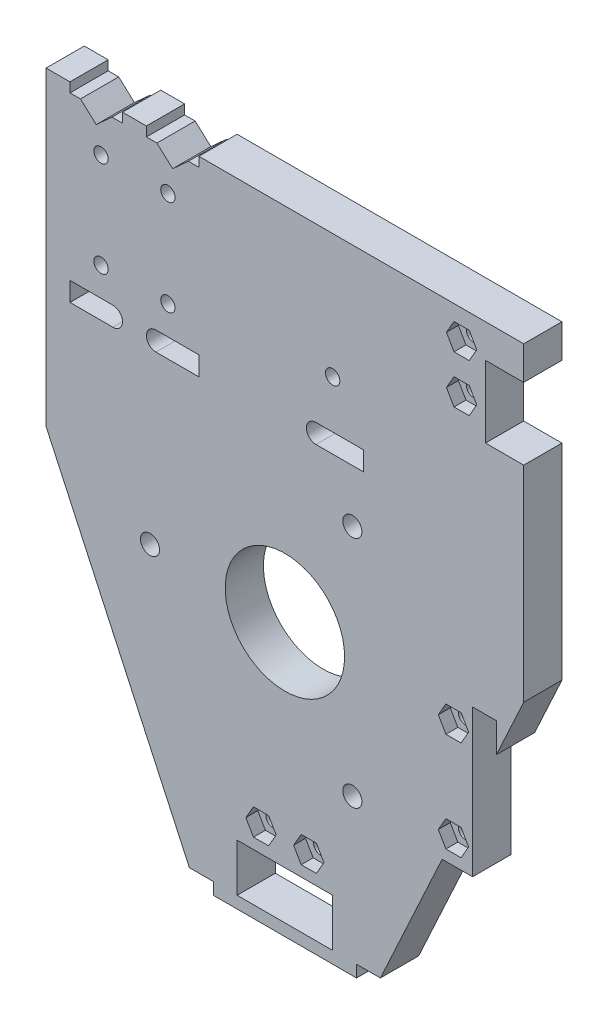
SolidWorks part; units mm, degrees
material "1060 合金"
ref_plane "前视基准面" through (0, 0, 0) normal (0, 0, 1) x (1, 0, 0)
ref_plane "上视基准面" through (0, 0, 0) normal (0, 1, 0) x (1, 0, 0)
ref_plane "右视基准面" through (0, 0, 0) normal (1, 0, 0) x (0, 0, -1)
sketch "草图1" plane through (0, 0, 0) normal (0, 0, 1) x (1, 0, 0)
  line L1 (0, 0) -> (100, 0)
  line L2 (0, 0) -> (0, 130)
  line L3 (0, 130) -> (100, 130)
  line L4 (100, 0) -> (100, 130)
  dimension "D1" = 100
  dimension "D2" = 130
extrude "凸台-拉伸1" add sketch "草图1" along normal blind 8
sketch "草图2" plane through (0, 0, 8) normal (0, 0, 1) x (1, 0, 0)
  line L0 (0, 130) -> (0, 0) construction
  line L1 (0, 0) -> (100, 0) construction
  circle A0 centre (50, 54.5) radius 25
  dimension "D1" = 50
  dimension "D2" = 50
  dimension "D3" = 54.5
sketch "草图3" plane through (0, 0, 8) normal (0, 0, 1) x (1, 0, 0)
  line L0 (0, 0) -> (100, 0) construction
  line L1 (40, 0) -> (60, 0)
  line L2 (40, 0) -> (40, 10)
  line L3 (40, 10) -> (60, 10)
  line L4 (60, 0) -> (60, 10)
  line L5 (0, 130) -> (0, 0) construction
  line L6 (0, 0) -> (30, 0)
  line L7 (30, 0) -> (0, 65)
  line L8 (0, 65) -> (0, 0)
  line L9 (100, 0) -> (100, 65)
  line L10 (100, 0) -> (100, 130) construction
  line L11 (100, 65) -> (70, 0)
  line L12 (70, 0) -> (100, 0)
  dimension "D1" = 20
  dimension "D2" = 10
  dimension "D3" = 40
  dimension "D4" = 30
  dimension "D5" = 30
extrude "切除-拉伸1" cut sketch "草图3" against normal blind 8
sketch "草图4" plane through (0, 0, 0) normal (0, 0, -1) x (-1, 0, 0)
  line L0 (-56.5, 94) -> (-66.5, 94)
  line L1 (-100, 65) -> (-100, 130) construction
  line L2 (-100, 108) -> (-92, 108)
  line L3 (-100, 108) -> (-100, 123)
  line L4 (-100, 123) -> (-92, 123)
  line L5 (-66.5, 94) -> (-66.5, 90)
  line L6 (-66.5, 90) -> (-56.5, 90)
  line L7 (-32, 94) -> (-32, 90)
  line L8 (-32, 90) -> (-23, 90)
  line L9 (-23, 94) -> (-32, 94)
  line L10 (-5, 94) -> (-5, 90)
  line L11 (-5, 90) -> (-14, 90)
  line L12 (-14, 94) -> (-5, 94)
  line L13 (-10.5, 125) -> (-13.8, 128)
  line L14 (-100, 130) -> (0, 130) construction
  line L15 (-13.8, 128) -> (-10.5, 125) construction
  line L16 (-16, 130) -> (-5, 130)
  line L17 (-10.5, 125) -> (-7.2, 128) construction
  line L18 (-7.2, 128) -> (-10.5, 125)
  line L19 (-26.5, 125) -> (-29.8, 128)
  line L20 (-29.8, 128) -> (-26.5, 125) construction
  line L21 (-32, 130) -> (-21, 130)
  line L22 (-26.5, 125) -> (-23.2, 128) construction
  line L23 (-23.2, 128) -> (-26.5, 125)
  line L24 (-21, 130) -> (-21, 128)
  line L25 (-92, 108) -> (-92, 123)
  line L26 (-100, 108) -> (-80, 108) construction
  line L27 (-21, 128) -> (-23.2, 128)
  line L28 (-32, 128) -> (-32, 130)
  line L29 (-29.8, 128) -> (-32, 128)
  line L30 (-5, 130) -> (-5, 128)
  line L31 (-5, 128) -> (-7.2, 128)
  line L32 (-60, 10) -> (-40, 10) construction
  line L33 (-13.8, 128) -> (-16, 128)
  line L34 (-16, 128) -> (-16, 130)
  line L35 (-40, 10) -> (-40, 0) construction
  line L36 (-60, 0) -> (-60, 10) construction
  arc A0 (-56.5, 90) -> (-56.5, 94) centre (-56.5, 92) ccw
  arc A1 (-23, 90) -> (-23, 94) centre (-23, 92) ccw
  arc A2 (-14, 90) -> (-14, 94) centre (-14, 92) cw
  circle A4 centre (-87, 124) radius 1.5
  circle A5 centre (-25.5, 100) radius 1.5
  circle A6 centre (-11.5, 100) radius 1.5
  circle A7 centre (-11.5, 120) radius 1.5
  circle A8 centre (-25.5, 120) radius 1.5
  circle A9 centre (-60, 104) radius 1.5
  circle A10 centre (-45, 15) radius 1.5
  circle A11 centre (-55, 15) radius 1.5
  circle A15 centre (-87, 114) radius 1.5
  dimension "D1" = 5
  dimension "D2" = 5
  dimension "D3" = 5
  dimension "D4" = 5
extrude "切除-拉伸2" cut sketch "草图4" against normal through all
sketch "草图9" plane through (0, 0, 8) normal (0, 0, 1) x (1, 0, 0)
  line L1 (90.1754, 124) -> (88.5877, 126.75)
  line L2 (88.5877, 126.75) -> (85.4123, 126.75)
  line L3 (85.4123, 126.75) -> (83.8246, 124)
  line L4 (83.8246, 124) -> (85.4123, 121.25)
  line L5 (85.4123, 121.25) -> (88.5877, 121.25)
  line L6 (88.5877, 121.25) -> (90.1754, 124)
  line L7 (90.1754, 114) -> (88.5877, 116.75)
  line L8 (88.5877, 116.75) -> (85.4123, 116.75)
  line L9 (85.4123, 116.75) -> (83.8246, 114)
  line L10 (83.8246, 114) -> (85.4123, 111.25)
  line L11 (85.4123, 111.25) -> (88.5877, 111.25)
  line L12 (88.5877, 111.25) -> (90.1754, 114)
  line L13 (48.1754, 15) -> (46.5877, 17.75)
  line L14 (46.5877, 17.75) -> (43.4123, 17.75)
  line L15 (43.4123, 17.75) -> (41.8246, 15)
  line L16 (41.8246, 15) -> (43.4123, 12.25)
  line L17 (43.4123, 12.25) -> (46.5877, 12.25)
  line L18 (46.5877, 12.25) -> (48.1754, 15)
  line L19 (58.1754, 15) -> (56.5877, 17.75)
  line L20 (56.5877, 17.75) -> (53.4123, 17.75)
  line L21 (53.4123, 17.75) -> (51.8246, 15)
  line L22 (51.8246, 15) -> (53.4123, 12.25)
  line L23 (53.4123, 12.25) -> (56.5877, 12.25)
  line L24 (56.5877, 12.25) -> (58.1754, 15)
  circle A0 centre (45, 15) radius 2.75 construction
  circle A1 centre (55, 15) radius 2.75 construction
  circle A2 centre (87, 124) radius 2.75 construction
  circle A3 centre (87, 114) radius 2.75 construction
  dimension "D1" = 5.5
  dimension "D2" = 5.5
  dimension "D3" = 5.5
  dimension "D4" = 5.5
extrude "切除-拉伸6" cut sketch "草图9" against normal blind 2.5
sketch "草图10" plane through (0, 0, 8) normal (0, 0, 1) x (1, 0, 0)
  line L0 (94.3, 58.8) -> (89.3, 58.8)
  line L1 (89.3, 58.8) -> (89.3, 28)
  line L2 (89.3, 28) -> (94.3, 28)
  line L3 (94.3, 28) -> (94.3, 58.8)
  circle A0 centre (50, 54.5) radius 12.5
  dimension "D1" = 25
extrude "切除-拉伸7" cut sketch "草图10" against normal through all
sketch "草图12" plane through (0, 0, 8) normal (0, 0, 1) x (1, 0, 0)
  line L0 (89.3, 41.8167) -> (82.9231, 28)
  line L1 (89.3, 41.8167) -> (70, 0) construction
  line L2 (81.3, 28) -> (94.3, 28) construction
  line L3 (82.9231, 28) -> (89.3, 28)
  line L4 (89.3, 28) -> (89.3, 41.8167)
extrude "凸台-拉伸3" add sketch "草图12" against normal blind 8
sketch "草图5" plane through (0, 0, 8) normal (0, 0, 1) x (1, 0, 0)
  circle A0 centre (21.75, 54.5) radius 2
  circle A1 centre (64.125, 78.9652) radius 2
  circle A2 centre (64.125, 30.0348) radius 2
  circle A3 centre (50, 54.5) radius 12.5 construction
  circle A4 centre (85.3, 53.8) radius 1.5
  circle A5 centre (85.3, 33) radius 1.5
  dimension "D2" = 4
  dimension "D1" = 28.25
  dimension "D3" = 0
  dimension "D4" = 3
extrude "切除-拉伸3" cut sketch "草图5" against normal through all
sketch "草图11" plane through (0, 0, 8) normal (0, 0, 1) x (1, 0, 0)
  line L0 (30, 0) -> (40, 0) construction
  line L1 (35, 0) -> (65, 0)
  line L2 (35, 0) -> (35, -2.5)
  line L3 (35, -2.5) -> (65, -2.5)
  line L4 (65, 0) -> (65, -2.5)
  dimension "D1" = 2.5
extrude "凸台-拉伸2" add sketch "草图11" against normal blind 8
sketch "草图14" plane through (0, 0, 8) normal (0, 0, 1) x (1, 0, 0)
  line L1 (88.4754, 53.8) -> (86.8877, 56.55)
  line L2 (86.8877, 56.55) -> (83.7123, 56.55)
  line L3 (83.7123, 56.55) -> (82.1246, 53.8)
  line L4 (82.1246, 53.8) -> (83.7123, 51.05)
  line L5 (83.7123, 51.05) -> (86.8877, 51.05)
  line L6 (86.8877, 51.05) -> (88.4754, 53.8)
  line L7 (88.4754, 33) -> (86.8877, 35.75)
  line L8 (86.8877, 35.75) -> (83.7123, 35.75)
  line L9 (83.7123, 35.75) -> (82.1246, 33)
  line L10 (82.1246, 33) -> (83.7123, 30.25)
  line L11 (83.7123, 30.25) -> (86.8877, 30.25)
  line L12 (86.8877, 30.25) -> (88.4754, 33)
  circle A0 centre (85.3, 53.8) radius 2.75 construction
  circle A1 centre (85.3, 33) radius 2.75 construction
  dimension "D1" = 5.5
  dimension "D2" = 5.5
extrude "切除-拉伸8" cut sketch "草图14" against normal blind 2.5
